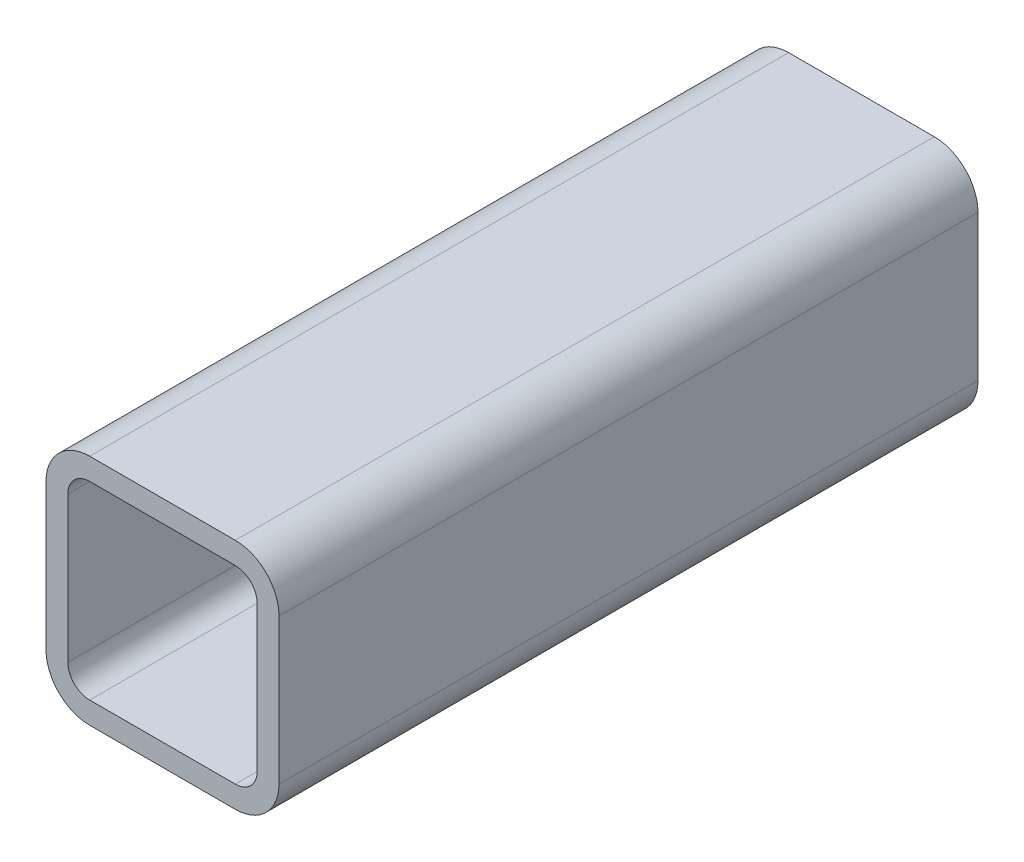
SolidWorks part; units mm, degrees
ref_plane "Plane1" through (0, 0, 0) normal (0, 0, 1) x (1, 0, 0)
ref_plane "Plane2" through (0, 0, 0) normal (0, 1, 0) x (1, 0, 0)
ref_plane "Plane3" through (0, 0, 0) normal (1, 0, 0) x (0, 0, -1)
sketch "Sketch1" plane through (0, 0, 0) normal (0, 0, 1) x (1, 0, 0)
  line L0 (9.525, 4.7625) -> (41.275, 4.7625)
  line L1 (4.7625, 9.525) -> (4.7625, 41.275)
  line L2 (41.275, 46.0375) -> (9.525, 46.0375)
  line L3 (46.0375, 41.275) -> (46.0375, 9.525)
  line L4 (9.525, 0) -> (41.275, 0)
  line L5 (0, 9.525) -> (0, 41.275)
  line L6 (41.275, 50.8) -> (9.525, 50.8)
  line L7 (50.8, 41.275) -> (50.8, 9.525)
  arc A0 (50.8, 41.275) -> (41.275, 50.8) centre (41.275, 41.275) ccw
  arc A1 (41.275, 0) -> (50.8, 9.525) centre (41.275, 9.525) ccw
  arc A2 (0, 9.525) -> (9.525, 0) centre (9.525, 9.525) ccw
  arc A3 (9.525, 50.8) -> (0, 41.275) centre (9.525, 41.275) ccw
  arc A4 (9.525, 46.0375) -> (4.7625, 41.275) centre (9.525, 41.275) ccw
  arc A5 (46.0375, 41.275) -> (41.275, 46.0375) centre (41.275, 41.275) ccw
  arc A6 (41.275, 4.7625) -> (46.0375, 9.525) centre (41.275, 9.525) ccw
  arc A7 (4.7625, 9.525) -> (9.525, 4.7625) centre (9.525, 9.525) ccw
  dimension "D1" = 9.525
  dimension "Thickness" = 4.7625
  dimension "V_leg" = 50.8
  dimension "H_leg" = 50.8
extrude "BaseTubeS" add sketch "Sketch1" along normal mid plane 152.4
equation "\"D1@Sketch1\" = \"Thickness@Sketch1\" * 2"
